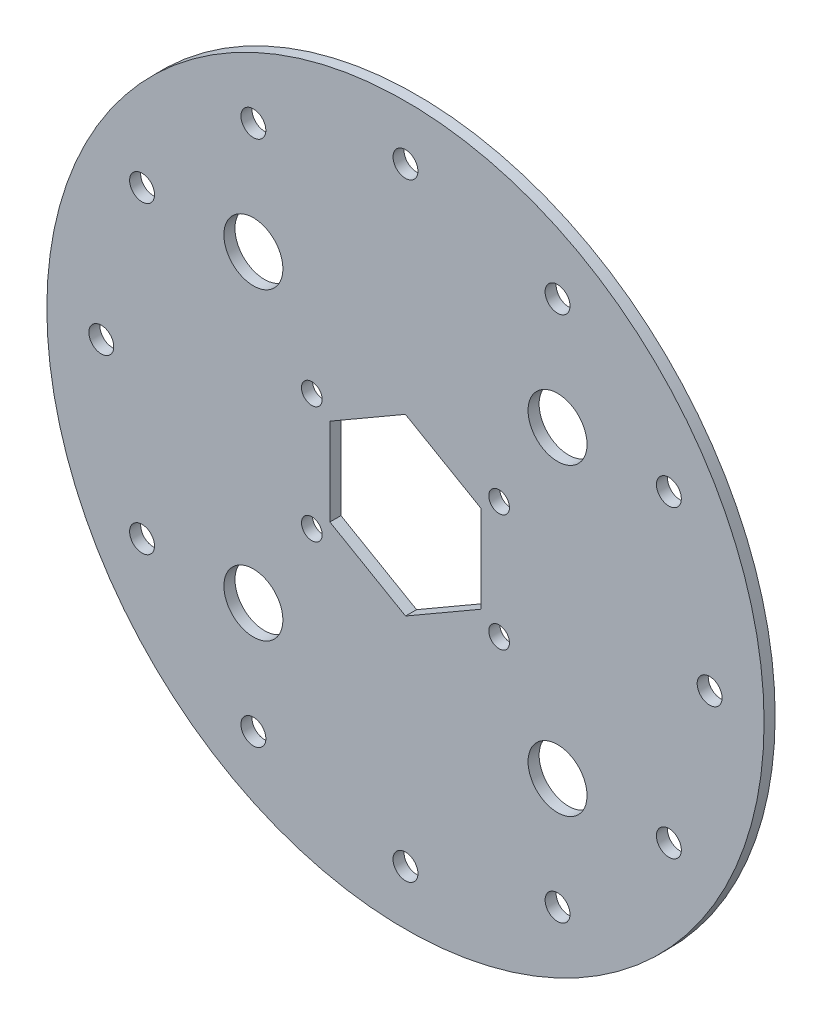
SolidWorks part; units mm, degrees
material "6061-T6 (SS)"
ref_plane "Front Plane" through (0, 0, 0) normal (0, 0, 1) x (1, 0, 0)
ref_plane "Top Plane" through (0, 0, 0) normal (0, 1, 0) x (1, 0, 0)
ref_plane "Right Plane" through (0, 0, 0) normal (1, 0, 0) x (0, 0, -1)
sketch "Sketch1" plane through (0, 0, 0) normal (0, 0, 1) x (1, 0, 0)
  line L5 (36.236, -23.1833) -> (36.236, -113.1833) construction
  line L6 (36.236, -23.1833) -> (133.516, -23.1833) construction
  line L7 (15.736, -35.0328) -> (36.2479, -46.8616)
  line L8 (36.2479, -46.8616) -> (56.7479, -35.0121)
  line L9 (56.7479, -35.0121) -> (56.736, -11.3338)
  line L10 (56.736, -11.3338) -> (36.224, 0.495)
  line L11 (36.224, 0.495) -> (15.724, -11.3546)
  line L12 (15.724, -11.3546) -> (15.736, -35.0328)
  circle A0 centre (36.236, -23.1833) radius 82.5 construction
  circle A1 centre (36.236, -23.1833) radius 20.5 construction
  circle A2 centre (-46.264, -23.1833) radius 3.175 construction
  circle A3 centre (-35.2111, 18.0667) radius 3.175 construction
  circle A4 centre (-5.014, 48.2638) radius 3.175 construction
  circle A5 centre (36.236, 59.3167) radius 3.175 construction
  circle A6 centre (77.486, 48.2638) radius 3.175 construction
  circle A7 centre (107.6831, 18.0667) radius 3.175 construction
  circle A8 centre (118.736, -23.1833) radius 3.175 construction
  circle A9 centre (107.6831, -64.4333) radius 3.175 construction
  circle A10 centre (77.486, -94.6304) radius 3.175 construction
  circle A11 centre (36.236, -105.6833) radius 3.175 construction
  circle A12 centre (-5.014, -94.6304) radius 3.175 construction
  circle A13 centre (-35.2111, -64.4333) radius 3.175 construction
  circle A27 centre (36.236, -23.1833) radius 97.28
  circle A28 centre (61.636, -7.3083) radius 2.8067
  circle A29 centre (61.636, -39.0583) radius 2.8067
  circle A30 centre (10.836, -39.0583) radius 2.8067
  circle A31 centre (10.836, -7.3083) radius 2.8067
  circle A32 centre (36.236, -23.1833) radius 20.506 construction
  circle A33 centre (-5.014, -64.4333) radius 8
  circle A34 centre (77.486, -64.4333) radius 8
  circle A35 centre (77.486, 18.0667) radius 8
  circle A36 centre (-5.014, 18.0667) radius 8
  point P34 (36.236, -23.1833)
  dimension "D1" = 165
  dimension "D2" = 41
  dimension "D3" = 6.35
  dimension "D5" = 194.56
  dimension "D6" = 5.6134
  dimension "D9" = 16
  dimension "D7" = 15.875
  dimension "D8" = 25.4
  dimension "D4" = 12
extrude "Boss-Extrude1" add sketch "Sketch1" along normal blind 3
hole_wizard "1/4 Clearance Hole1" positions "Sketch4" profile "Sketch5" hole size "1/4" standard "ANSI Inch" end condition through all
sketch "Sketch4" plane through (0, 0, 0) normal (0, 0, -1) x (-1, 0, 0)
  point P0 (-118.736, -23.1833)
  point P3 (-107.6831, -64.4333)
  point P6 (46.264, -23.1833)
  point P9 (35.2111, -64.4333)
  point P12 (-77.486, -94.6304)
  point P15 (-36.236, -105.6833)
  point P18 (5.014, -94.6304)
  point P21 (35.2111, 18.0667)
  point P24 (5.014, 48.2638)
  point P27 (-36.236, 59.3167)
  point P30 (-77.486, 48.2638)
  point P33 (-107.6831, 18.0667)
sketch "Sketch5" plane through (118.736, -23.1833, 0) normal (1, 0, 0) x (0, 1, 0)
  line L0 (0, 0) -> (0, 3)
  line L1 (0, 3) -> (3.3782, 3)
  line L2 (3.3782, 3) -> (3.3782, 0)
  line L5 (3.3782, 0) -> (0, 0)
  line L11 (0, -6.35) -> (0, 107.95) construction
  dimension "Thru Hole Dia." = 6.7564
  dimension "Thru Hole Depth" = 3
